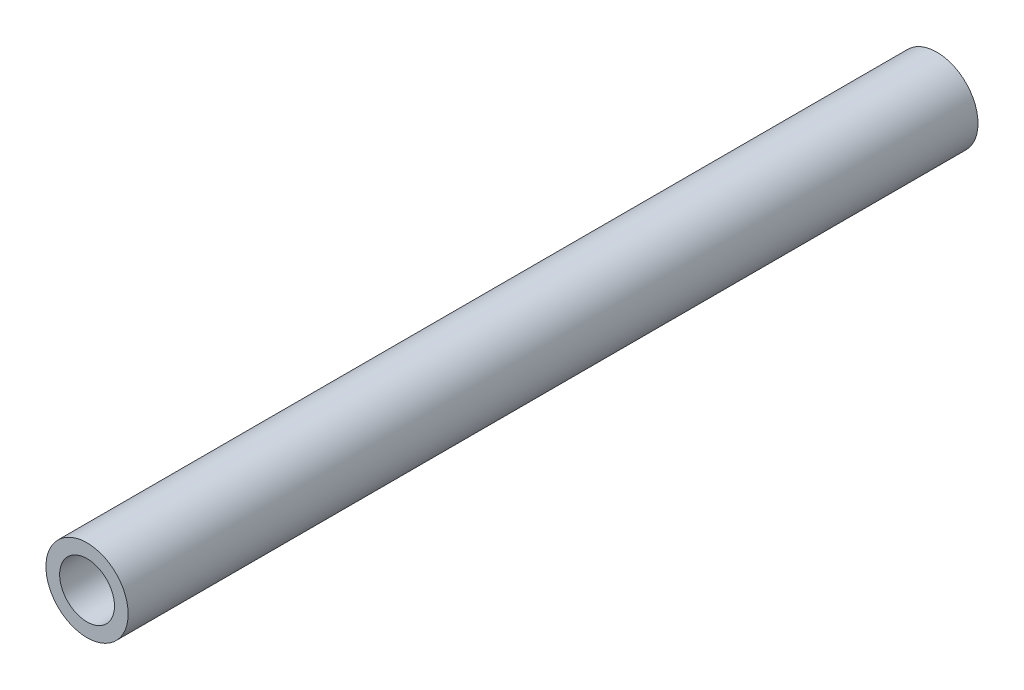
SolidWorks part; units mm, degrees
ref_plane "Front Plane" through (0, 0, 0) normal (0, 0, 1) x (1, 0, 0)
ref_plane "Top Plane" through (0, 0, 0) normal (0, 1, 0) x (1, 0, 0)
ref_plane "Right Plane" through (0, 0, 0) normal (1, 0, 0) x (0, 0, -1)
sketch "Sketch1" plane through (0, 0, 0) normal (0, 0, 1) x (1, 0, 0)
  circle A0 centre (0, 0) radius 2
  circle A1 centre (0, 0) radius 3
  dimension "D1" = 4
  dimension "D2" = 1
extrude "Boss-Extrude1" add sketch "Sketch1" along normal blind 62
